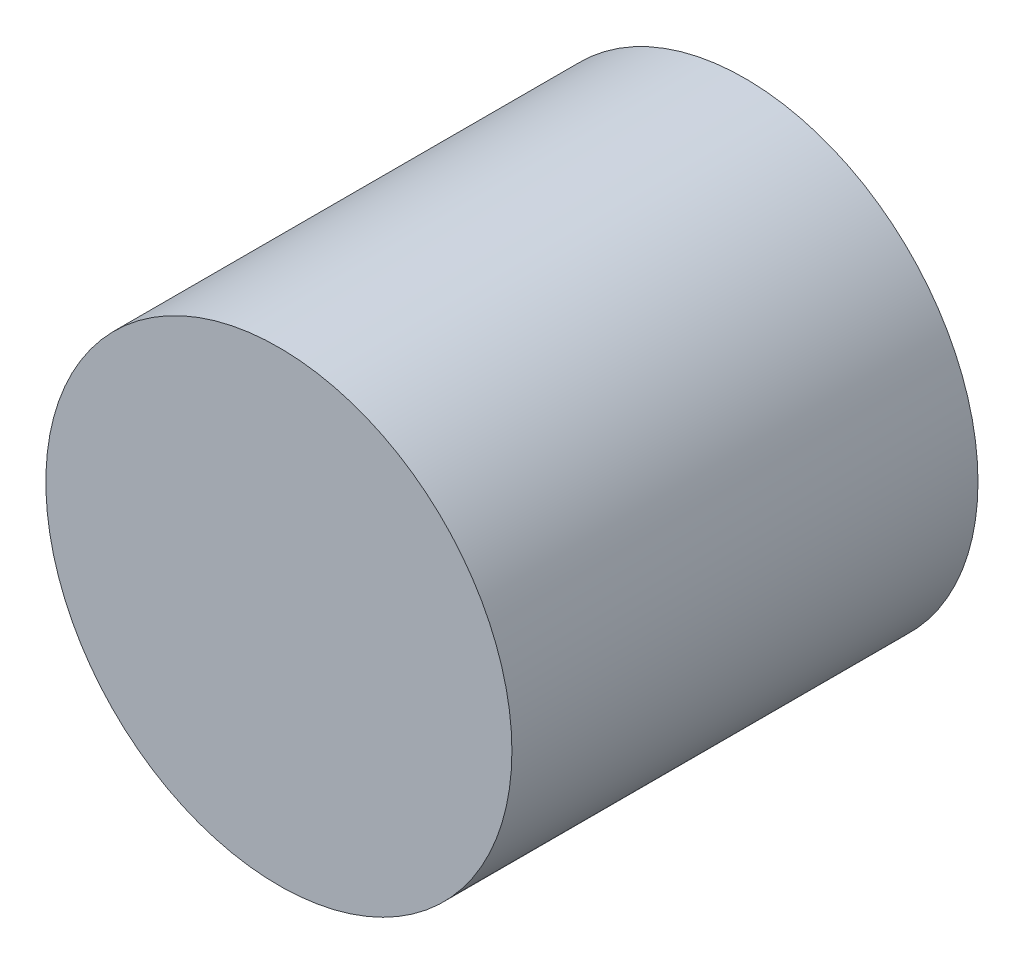
SolidWorks part; units mm, degrees
ref_plane "Спереди" through (0, 0, 0) normal (0, 0, 1) x (1, 0, 0)
ref_plane "Сверху" through (0, 0, 0) normal (0, 1, 0) x (1, 0, 0)
ref_plane "Справа" through (0, 0, 0) normal (1, 0, 0) x (0, 0, -1)
sketch "Эскиз1" plane through (0, 0, 0) normal (0, 0, 1) x (1, 0, 0)
  circle A0 centre (0, 0) radius 10
extrude "Бобышка-Вытянуть1" add sketch "Эскиз1" along normal blind 20 contours A0
